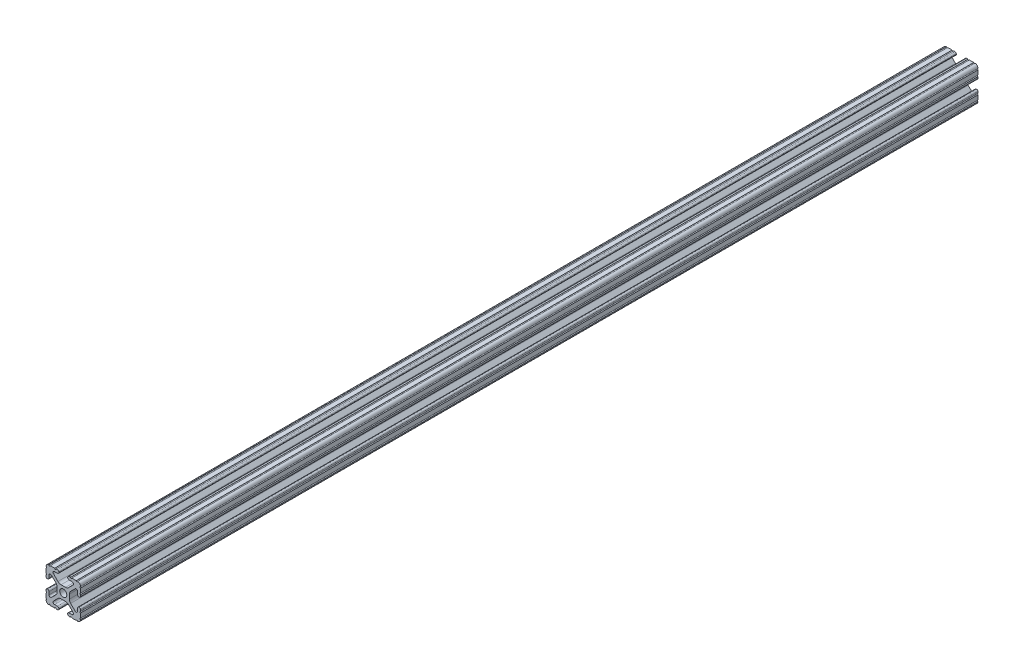
SolidWorks part; units mm, degrees
ref_plane "Front" through (0, 0, 0) normal (0, 0, 1) x (1, 0, 0)
ref_plane "Top" through (0, 0, 0) normal (0, 1, 0) x (1, 0, 0)
ref_plane "Right" through (0, 0, 0) normal (1, 0, 0) x (0, 0, -1)
sketch "Sketch1" plane through (0, 0, 0) normal (0, 0, 1) x (1, 0, 0)
  line L0 (-7.5107, 9.4563) -> (7.5107, 9.4563) construction
  line L1 (-7.4968, -9.4098) -> (7.4968, -9.4098) construction
  line L88 (-7.1797, -8.6452) -> (-3.9523, -5.4237)
  line L89 (-1.7093, -4.4958) -> (1.7093, -4.4958)
  line L90 (3.9523, -5.4237) -> (7.1797, -8.6452)
  line L91 (6.4164, -10.4902) -> (4.2875, -10.4902)
  line L92 (3.2385, -11.5392) -> (3.2385, -11.651)
  line L93 (4.2875, -12.7) -> (5.3171, -12.7)
  line L94 (6.3331, -12.7) -> (9.5504, -12.7)
  line L95 (12.7, -9.5504) -> (12.7, -6.3331)
  line L96 (12.7, -5.3171) -> (12.7, -4.2875)
  line L97 (11.651, -3.2385) -> (11.5392, -3.2385)
  line L98 (10.4902, -4.2875) -> (10.4902, -6.4021)
  line L99 (8.7371, -7.1294) -> (5.441, -3.8408)
  line L100 (4.5085, -1.5932) -> (4.5085, 1.5932)
  line L101 (5.441, 3.8408) -> (8.7371, 7.1294)
  line L102 (10.4902, 6.4021) -> (10.4902, 4.2875)
  line L103 (11.5392, 3.2385) -> (11.651, 3.2385)
  line L104 (12.7, 4.2875) -> (12.7, 5.3171)
  line L105 (12.7, 6.3331) -> (12.7, 9.5504)
  line L106 (9.5504, 12.7) -> (6.3331, 12.7)
  line L107 (5.3171, 12.7) -> (4.2875, 12.7)
  line L108 (3.2385, 11.651) -> (3.2385, 11.5392)
  line L109 (4.2875, 10.4902) -> (6.4768, 10.4902)
  line L110 (7.207, 8.7244) -> (3.8983, 5.4232)
  line L111 (1.6558, 4.4958) -> (-1.6558, 4.4958)
  line L112 (-3.8983, 5.4232) -> (-7.207, 8.7244)
  line L113 (-6.4768, 10.4902) -> (-4.2875, 10.4902)
  line L114 (-3.2385, 11.5392) -> (-3.2385, 11.651)
  line L115 (-4.2875, 12.7) -> (-5.3171, 12.7)
  line L116 (-6.3331, 12.7) -> (-9.5504, 12.7)
  line L117 (-12.7, 9.5504) -> (-12.7, 6.3331)
  line L118 (-12.7, 5.3171) -> (-12.7, 4.2875)
  line L119 (-11.651, 3.2385) -> (-11.5392, 3.2385)
  line L120 (-10.4902, 4.2875) -> (-10.4902, 6.4021)
  line L121 (-8.7371, 7.1294) -> (-5.441, 3.8408)
  line L122 (-4.5085, 1.5932) -> (-4.5085, -1.5932)
  line L123 (-5.441, -3.8408) -> (-8.7371, -7.1294)
  line L124 (-10.4902, -6.4021) -> (-10.4902, -4.2875)
  line L125 (-11.5392, -3.2385) -> (-11.651, -3.2385)
  line L126 (-12.7, -4.2875) -> (-12.7, -5.3171)
  line L127 (-12.7, -6.3331) -> (-12.7, -9.5504)
  line L128 (-9.5504, -12.7) -> (-6.3331, -12.7)
  line L129 (-5.3171, -12.7) -> (-4.2875, -12.7)
  line L130 (-3.2385, -11.651) -> (-3.2385, -11.5392)
  line L131 (-4.2875, -10.4902) -> (-6.4164, -10.4902)
  circle A1 centre (0, 0) radius 2.6035
  arc A104 (-7.1797, -8.6452) -> (-6.4164, -10.4902) centre (-6.4164, -9.4098) ccw
  arc A105 (-1.7093, -4.4958) -> (-3.9523, -5.4237) centre (-1.7093, -7.6708) ccw
  arc A106 (3.9523, -5.4237) -> (1.7093, -4.4958) centre (1.7093, -7.6708) ccw
  arc A107 (6.4164, -10.4902) -> (7.1797, -8.6452) centre (6.4164, -9.4098) ccw
  arc A108 (4.2875, -10.4902) -> (3.2385, -11.5392) centre (4.2875, -11.5392) ccw
  arc A109 (3.2385, -11.651) -> (4.2875, -12.7) centre (4.2875, -11.651) ccw
  arc A110 (6.3331, -12.7) -> (5.3171, -12.7) centre (5.8251, -12.7) ccw
  arc A111 (10.5664, -12.6998) -> (9.5504, -12.7) centre (10.0584, -12.7) ccw
  arc A112 (10.5664, -12.6998) -> (12.6998, -10.5664) centre (10.5918, -10.5918) ccw
  arc A113 (12.7, -9.5504) -> (12.6998, -10.5664) centre (12.7, -10.0584) ccw
  arc A114 (12.7, -5.3171) -> (12.7, -6.3331) centre (12.7, -5.8251) ccw
  arc A115 (12.7, -4.2875) -> (11.651, -3.2385) centre (11.651, -4.2875) ccw
  arc A116 (11.5392, -3.2385) -> (10.4902, -4.2875) centre (11.5392, -4.2875) ccw
  arc A117 (8.7371, -7.1294) -> (10.4902, -6.4021) centre (9.4628, -6.4021) ccw
  arc A118 (4.5085, -1.5932) -> (5.441, -3.8408) centre (7.6835, -1.5932) ccw
  arc A119 (5.441, 3.8408) -> (4.5085, 1.5932) centre (7.6835, 1.5932) ccw
  arc A120 (10.4902, 6.4021) -> (8.7371, 7.1294) centre (9.4628, 6.4021) ccw
  arc A121 (10.4902, 4.2875) -> (11.5392, 3.2385) centre (11.5392, 4.2875) ccw
  arc A122 (11.651, 3.2385) -> (12.7, 4.2875) centre (11.651, 4.2875) ccw
  arc A123 (12.7, 6.3331) -> (12.7, 5.3171) centre (12.7, 5.8251) ccw
  arc A124 (12.6998, 10.5664) -> (12.7, 9.5504) centre (12.7, 10.0584) ccw
  arc A125 (12.6998, 10.5664) -> (10.5664, 12.6998) centre (10.5918, 10.5918) ccw
  arc A126 (9.5504, 12.7) -> (10.5664, 12.6998) centre (10.0584, 12.7) ccw
  arc A127 (5.3171, 12.7) -> (6.3331, 12.7) centre (5.8251, 12.7) ccw
  arc A128 (4.2875, 12.7) -> (3.2385, 11.651) centre (4.2875, 11.651) ccw
  arc A129 (3.2385, 11.5392) -> (4.2875, 10.4902) centre (4.2875, 11.5392) ccw
  arc A130 (7.207, 8.7244) -> (6.4768, 10.4902) centre (6.4768, 9.4563) ccw
  arc A131 (1.6558, 4.4958) -> (3.8983, 5.4232) centre (1.6558, 7.6708) ccw
  arc A132 (-3.8983, 5.4232) -> (-1.6558, 4.4958) centre (-1.6558, 7.6708) ccw
  arc A133 (-6.4768, 10.4902) -> (-7.207, 8.7244) centre (-6.4768, 9.4563) ccw
  arc A134 (-4.2875, 10.4902) -> (-3.2385, 11.5392) centre (-4.2875, 11.5392) ccw
  arc A135 (-3.2385, 11.651) -> (-4.2875, 12.7) centre (-4.2875, 11.651) ccw
  arc A136 (-6.3331, 12.7) -> (-5.3171, 12.7) centre (-5.8251, 12.7) ccw
  arc A137 (-10.5664, 12.6998) -> (-9.5504, 12.7) centre (-10.0584, 12.7) ccw
  arc A138 (-10.5664, 12.6998) -> (-12.6998, 10.5664) centre (-10.5918, 10.5918) ccw
  arc A139 (-12.7, 9.5504) -> (-12.6998, 10.5664) centre (-12.7, 10.0584) ccw
  arc A140 (-12.7, 5.3171) -> (-12.7, 6.3331) centre (-12.7, 5.8251) ccw
  arc A141 (-12.7, 4.2875) -> (-11.651, 3.2385) centre (-11.651, 4.2875) ccw
  arc A142 (-11.5392, 3.2385) -> (-10.4902, 4.2875) centre (-11.5392, 4.2875) ccw
  arc A143 (-8.7371, 7.1294) -> (-10.4902, 6.4021) centre (-9.4628, 6.4021) ccw
  arc A144 (-4.5085, 1.5932) -> (-5.441, 3.8408) centre (-7.6835, 1.5932) ccw
  arc A145 (-5.441, -3.8408) -> (-4.5085, -1.5932) centre (-7.6835, -1.5932) ccw
  arc A146 (-10.4902, -6.4021) -> (-8.7371, -7.1294) centre (-9.4628, -6.4021) ccw
  arc A147 (-10.4902, -4.2875) -> (-11.5392, -3.2385) centre (-11.5392, -4.2875) ccw
  arc A148 (-11.651, -3.2385) -> (-12.7, -4.2875) centre (-11.651, -4.2875) ccw
  arc A149 (-12.7, -6.3331) -> (-12.7, -5.3171) centre (-12.7, -5.8251) ccw
  arc A150 (-12.6998, -10.5664) -> (-12.7, -9.5504) centre (-12.7, -10.0584) ccw
  arc A151 (-12.6998, -10.5664) -> (-10.5664, -12.6998) centre (-10.5918, -10.5918) ccw
  arc A152 (-9.5504, -12.7) -> (-10.5664, -12.6998) centre (-10.0584, -12.7) ccw
  arc A153 (-5.3171, -12.7) -> (-6.3331, -12.7) centre (-5.8251, -12.7) ccw
  arc A154 (-4.2875, -12.7) -> (-3.2385, -11.651) centre (-4.2875, -11.651) ccw
  arc A155 (-3.2385, -11.5392) -> (-4.2875, -10.4902) centre (-4.2875, -11.5392) ccw
extrude "Boss-Extrude1" add sketch "Sketch1" along normal mid plane 914.4
sketch "Sketch3" plane through (-12.7, 0, 0) normal (-1, 0, 0) x (0, 0, 1)
  line L0 (-203.2, -25.4) -> (-203.2, 21.1581) construction
  line L1 (-203.2, -27.5528) -> (-203.2, 21.1581)
  line L2 (-203.2, 21.1581) -> (-461.0909, 21.1581)
  line L3 (-461.0909, 21.1581) -> (-461.0909, -25.4)
  line L4 (-461.0909, -25.4) -> (-203.2, -27.5528)
extrude "Cut-Extrude2" cut sketch "Sketch3" against normal blind 26.924 and the other way blind 4.318
